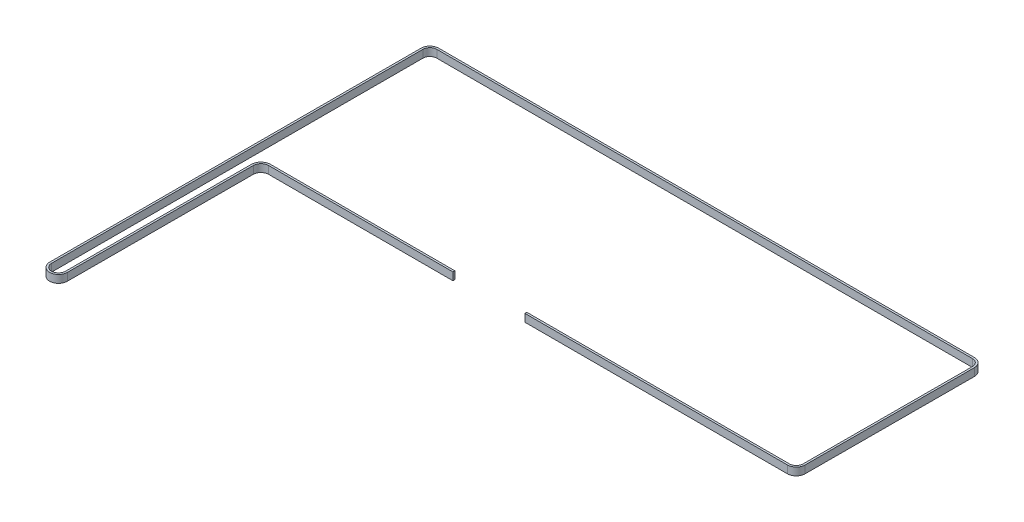
SolidWorks part; units mm, degrees
ref_plane "Front Plane" through (0, 0, 0) normal (0, 0, 1) x (1, 0, 0)
ref_plane "Top Plane" through (0, 0, 0) normal (0, 1, 0) x (1, 0, 0)
ref_plane "Right Plane" through (0, 0, 0) normal (1, 0, 0) x (0, 0, -1)
ref_plane "Plane1" through (0, 323, 0) normal (0, -1, 0) x (1, 0, 0)
sketch "Sketch1" plane through (0, 323, 0) normal (0, -1, 0) x (1, 0, 0)
  line L0 (-52.0251, -21.5073) -> (-195.6, -21.5073)
  line L1 (-201.6, -15.5198) -> (-201.9, 129.0143)
  line L2 (-215.7, 128.9928) -> (-215.4, -160.0072)
  line L3 (-208.5, -166.9) -> (208.8, -166.9)
  line L4 (215.7, -159.9843) -> (215.4, -28.4416)
  line L5 (208.5, -21.5573) -> (3.9749, -21.5573)
  line L6 (3.9749, -21.5573) -> (3.9749, -23.0573)
  line L7 (3.9749, -23.0573) -> (208.5, -23.0573)
  line L8 (213.9, -28.445) -> (214.2, -159.9877)
  line L9 (208.8, -165.4) -> (-208.5, -165.4)
  line L10 (-213.9, -160.0056) -> (-214.2, 128.9944)
  line L11 (-203.4, 129.0112) -> (-203.1, -15.5229)
  line L12 (-195.6, -23.0073) -> (-52.0251, -23.0073)
  line L13 (-52.0251, -23.0073) -> (-52.0251, -21.5073)
  arc A0 (-195.6, -21.5073) -> (-201.6, -15.5198) centre (-195.6, -15.5073) cw
  arc A1 (-201.9, 129.0143) -> (-215.7, 128.9928) centre (-208.8, 129) ccw
  arc A2 (-215.4, -160.0072) -> (-208.5, -166.9) centre (-208.5, -160) ccw
  arc A3 (208.8, -166.9) -> (215.7, -159.9843) centre (208.8, -160) ccw
  arc A4 (215.4, -28.4416) -> (208.5, -21.5573) centre (208.5, -28.4573) ccw
  arc A5 (208.5, -23.0573) -> (213.9, -28.445) centre (208.5, -28.4573) cw
  arc A6 (214.2, -159.9877) -> (208.8, -165.4) centre (208.8, -160) cw
  arc A7 (-208.5, -165.4) -> (-213.9, -160.0056) centre (-208.5, -160) cw
  arc A8 (-214.2, 128.9944) -> (-203.4, 129.0112) centre (-208.8, 129) cw
  arc A9 (-203.1, -15.5229) -> (-195.6, -23.0073) centre (-195.6, -15.5073) ccw
extrude "Boss-Extrude1" add sketch "Sketch1" against normal blind 6
